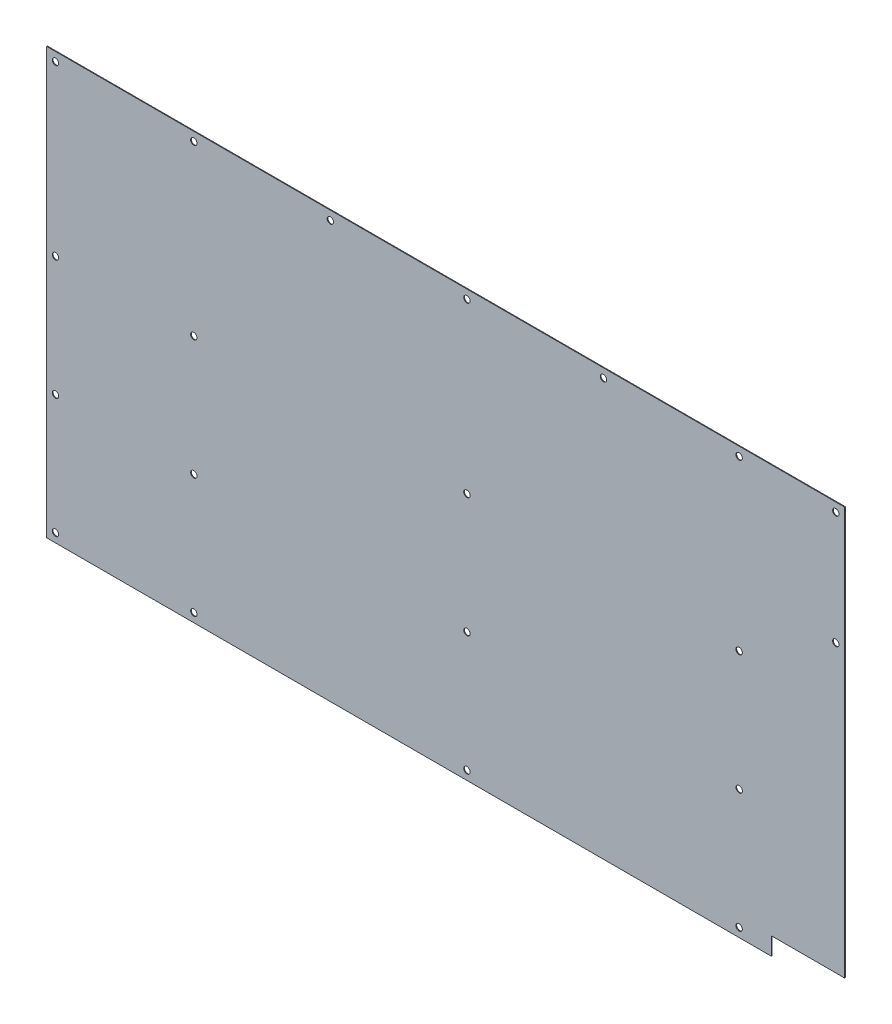
SolidWorks part; units mm, degrees
ref_plane "Front Plane" through (0, 0, 0) normal (0, 0, 1) x (1, 0, 0)
ref_plane "Top Plane" through (0, 0, 0) normal (0, 1, 0) x (1, 0, 0)
ref_plane "Right Plane" through (0, 0, 0) normal (1, 0, 0) x (0, 0, -1)
sketch "Model" plane through (0, 0, 0) normal (0, 0, 1) x (1, 0, 0)
  line L0 (0, 0) -> (415.29, 0)
  line L1 (415.29, 0) -> (415.29, 10.16)
  line L2 (415.29, 10.16) -> (457.2, 10.16)
  line L3 (457.2, 10.16) -> (457.2, 243.84)
  line L4 (457.2, 243.84) -> (0, 243.84)
  line L5 (0, 243.84) -> (0, 0)
  line L276 (452.12, 173.736) -> (452.12, 174.244)
  line L277 (451.866, 173.99) -> (452.374, 173.99)
  line L278 (452.12, 173.736) -> (452.12, 174.244)
  line L279 (451.866, 173.99) -> (452.374, 173.99)
  line L280 (452.12, 173.736) -> (452.12, 174.244)
  line L281 (451.866, 173.99) -> (452.374, 173.99)
  line L282 (452.12, 173.736) -> (452.12, 174.244)
  line L283 (451.866, 173.99) -> (452.374, 173.99)
  line L284 (452.12, 173.736) -> (452.12, 174.244)
  line L285 (451.866, 173.99) -> (452.374, 173.99)
  line L286 (452.12, 173.736) -> (452.12, 174.244)
  line L287 (451.866, 173.99) -> (452.374, 173.99)
  line L288 (452.12, 173.736) -> (452.12, 174.244)
  line L289 (451.866, 173.99) -> (452.374, 173.99)
  line L290 (452.12, 173.736) -> (452.12, 174.244)
  line L291 (451.866, 173.99) -> (452.374, 173.99)
  line L292 (452.12, 238.506) -> (452.12, 239.014)
  line L293 (451.866, 238.76) -> (452.374, 238.76)
  line L294 (452.12, 238.506) -> (452.12, 239.014)
  line L295 (451.866, 238.76) -> (452.374, 238.76)
  line L296 (452.12, 238.506) -> (452.12, 239.014)
  line L297 (451.866, 238.76) -> (452.374, 238.76)
  line L298 (452.12, 238.506) -> (452.12, 239.014)
  line L299 (451.866, 238.76) -> (452.374, 238.76)
  line L300 (452.12, 238.506) -> (452.12, 239.014)
  line L301 (451.866, 238.76) -> (452.374, 238.76)
  line L302 (452.12, 238.506) -> (452.12, 239.014)
  line L303 (451.866, 238.76) -> (452.374, 238.76)
  line L304 (452.12, 238.506) -> (452.12, 239.014)
  line L305 (451.866, 238.76) -> (452.374, 238.76)
  line L306 (452.12, 238.506) -> (452.12, 239.014)
  line L307 (451.866, 238.76) -> (452.374, 238.76)
  line L356 (5.08, 238.506) -> (5.08, 239.014)
  line L357 (4.826, 238.76) -> (5.334, 238.76)
  line L358 (5.08, 238.506) -> (5.08, 239.014)
  line L359 (4.826, 238.76) -> (5.334, 238.76)
  line L360 (5.08, 238.506) -> (5.08, 239.014)
  line L361 (4.826, 238.76) -> (5.334, 238.76)
  line L362 (5.08, 238.506) -> (5.08, 239.014)
  line L363 (4.826, 238.76) -> (5.334, 238.76)
  line L364 (5.08, 238.506) -> (5.08, 239.014)
  line L365 (4.826, 238.76) -> (5.334, 238.76)
  line L366 (5.08, 238.506) -> (5.08, 239.014)
  line L367 (4.826, 238.76) -> (5.334, 238.76)
  line L368 (5.08, 238.506) -> (5.08, 239.014)
  line L369 (4.826, 238.76) -> (5.334, 238.76)
  line L370 (5.08, 238.506) -> (5.08, 239.014)
  line L371 (4.826, 238.76) -> (5.334, 238.76)
  line L372 (84.328, 4.826) -> (84.328, 5.334)
  line L373 (84.074, 5.08) -> (84.582, 5.08)
  line L374 (84.328, 4.826) -> (84.328, 5.334)
  line L375 (84.074, 5.08) -> (84.582, 5.08)
  line L376 (84.328, 4.826) -> (84.328, 5.334)
  line L377 (84.074, 5.08) -> (84.582, 5.08)
  line L378 (84.328, 4.826) -> (84.328, 5.334)
  line L379 (84.074, 5.08) -> (84.582, 5.08)
  line L380 (84.328, 4.826) -> (84.328, 5.334)
  line L381 (84.074, 5.08) -> (84.582, 5.08)
  line L382 (84.328, 4.826) -> (84.328, 5.334)
  line L383 (84.074, 5.08) -> (84.582, 5.08)
  line L384 (84.328, 4.826) -> (84.328, 5.334)
  line L385 (84.074, 5.08) -> (84.582, 5.08)
  line L386 (84.328, 4.826) -> (84.328, 5.334)
  line L387 (84.074, 5.08) -> (84.582, 5.08)
  line L388 (84.328, 73.406) -> (84.328, 73.914)
  line L389 (84.074, 73.66) -> (84.582, 73.66)
  line L390 (84.328, 73.406) -> (84.328, 73.914)
  line L391 (84.074, 73.66) -> (84.582, 73.66)
  line L392 (84.328, 73.406) -> (84.328, 73.914)
  line L393 (84.074, 73.66) -> (84.582, 73.66)
  line L394 (84.328, 73.406) -> (84.328, 73.914)
  line L395 (84.074, 73.66) -> (84.582, 73.66)
  line L396 (84.328, 73.406) -> (84.328, 73.914)
  line L397 (84.074, 73.66) -> (84.582, 73.66)
  line L398 (84.328, 73.406) -> (84.328, 73.914)
  line L399 (84.074, 73.66) -> (84.582, 73.66)
  line L400 (84.328, 73.406) -> (84.328, 73.914)
  line L401 (84.074, 73.66) -> (84.582, 73.66)
  line L402 (84.328, 73.406) -> (84.328, 73.914)
  line L403 (84.074, 73.66) -> (84.582, 73.66)
  line L404 (84.328, 141.986) -> (84.328, 142.494)
  line L405 (84.074, 142.24) -> (84.582, 142.24)
  line L406 (84.328, 141.986) -> (84.328, 142.494)
  line L407 (84.074, 142.24) -> (84.582, 142.24)
  line L408 (84.328, 141.986) -> (84.328, 142.494)
  line L409 (84.074, 142.24) -> (84.582, 142.24)
  line L410 (84.328, 141.986) -> (84.328, 142.494)
  line L411 (84.074, 142.24) -> (84.582, 142.24)
  line L412 (84.328, 141.986) -> (84.328, 142.494)
  line L413 (84.074, 142.24) -> (84.582, 142.24)
  line L414 (84.328, 141.986) -> (84.328, 142.494)
  line L415 (84.074, 142.24) -> (84.582, 142.24)
  line L416 (84.328, 141.986) -> (84.328, 142.494)
  line L417 (84.074, 142.24) -> (84.582, 142.24)
  line L418 (84.328, 141.986) -> (84.328, 142.494)
  line L419 (84.074, 142.24) -> (84.582, 142.24)
  line L420 (84.328, 238.506) -> (84.328, 239.014)
  line L421 (84.074, 238.76) -> (84.582, 238.76)
  line L422 (84.328, 238.506) -> (84.328, 239.014)
  line L423 (84.074, 238.76) -> (84.582, 238.76)
  line L424 (84.328, 238.506) -> (84.328, 239.014)
  line L425 (84.074, 238.76) -> (84.582, 238.76)
  line L426 (84.328, 238.506) -> (84.328, 239.014)
  line L427 (84.074, 238.76) -> (84.582, 238.76)
  line L428 (84.328, 238.506) -> (84.328, 239.014)
  line L429 (84.074, 238.76) -> (84.582, 238.76)
  line L430 (84.328, 238.506) -> (84.328, 239.014)
  line L431 (84.074, 238.76) -> (84.582, 238.76)
  line L432 (84.328, 238.506) -> (84.328, 239.014)
  line L433 (84.074, 238.76) -> (84.582, 238.76)
  line L434 (84.328, 238.506) -> (84.328, 239.014)
  line L435 (84.074, 238.76) -> (84.582, 238.76)
  line L484 (162.56, 238.506) -> (162.56, 239.014)
  line L485 (162.306, 238.76) -> (162.814, 238.76)
  line L486 (162.56, 238.506) -> (162.56, 239.014)
  line L487 (162.306, 238.76) -> (162.814, 238.76)
  line L488 (162.56, 238.506) -> (162.56, 239.014)
  line L489 (162.306, 238.76) -> (162.814, 238.76)
  line L490 (162.56, 238.506) -> (162.56, 239.014)
  line L491 (162.306, 238.76) -> (162.814, 238.76)
  line L492 (162.56, 238.506) -> (162.56, 239.014)
  line L493 (162.306, 238.76) -> (162.814, 238.76)
  line L494 (162.56, 238.506) -> (162.56, 239.014)
  line L495 (162.306, 238.76) -> (162.814, 238.76)
  line L496 (162.56, 238.506) -> (162.56, 239.014)
  line L497 (162.306, 238.76) -> (162.814, 238.76)
  line L498 (162.56, 238.506) -> (162.56, 239.014)
  line L499 (162.306, 238.76) -> (162.814, 238.76)
  line L500 (240.7699, 4.827) -> (240.8141, 5.333)
  line L501 (240.539, 5.1021) -> (241.045, 5.0579)
  line L502 (240.7699, 4.827) -> (240.8141, 5.333)
  line L503 (240.539, 5.1021) -> (241.045, 5.0579)
  line L504 (240.7699, 4.827) -> (240.8141, 5.333)
  line L505 (240.539, 5.1021) -> (241.045, 5.0579)
  line L506 (240.7699, 4.827) -> (240.8141, 5.333)
  line L507 (240.539, 5.1021) -> (241.045, 5.0579)
  line L508 (240.7699, 4.827) -> (240.8141, 5.333)
  line L509 (240.539, 5.1021) -> (241.045, 5.0579)
  line L510 (240.7699, 4.827) -> (240.8141, 5.333)
  line L511 (240.539, 5.1021) -> (241.045, 5.0579)
  line L512 (240.7699, 4.827) -> (240.8141, 5.333)
  line L513 (240.539, 5.1021) -> (241.045, 5.0579)
  line L514 (240.7699, 4.827) -> (240.8141, 5.333)
  line L515 (240.539, 5.1021) -> (241.045, 5.0579)
  line L516 (240.792, 73.406) -> (240.792, 73.914)
  line L517 (240.538, 73.66) -> (241.046, 73.66)
  line L518 (240.792, 73.406) -> (240.792, 73.914)
  line L519 (240.538, 73.66) -> (241.046, 73.66)
  line L520 (240.792, 73.406) -> (240.792, 73.914)
  line L521 (240.538, 73.66) -> (241.046, 73.66)
  line L522 (240.792, 73.406) -> (240.792, 73.914)
  line L523 (240.538, 73.66) -> (241.046, 73.66)
  line L524 (240.792, 73.406) -> (240.792, 73.914)
  line L525 (240.538, 73.66) -> (241.046, 73.66)
  line L526 (240.792, 73.406) -> (240.792, 73.914)
  line L527 (240.538, 73.66) -> (241.046, 73.66)
  line L528 (240.792, 73.406) -> (240.792, 73.914)
  line L529 (240.538, 73.66) -> (241.046, 73.66)
  line L530 (240.792, 73.406) -> (240.792, 73.914)
  line L531 (240.538, 73.66) -> (241.046, 73.66)
  line L532 (240.792, 141.986) -> (240.792, 142.494)
  line L533 (240.538, 142.24) -> (241.046, 142.24)
  line L534 (240.792, 141.986) -> (240.792, 142.494)
  line L535 (240.538, 142.24) -> (241.046, 142.24)
  line L536 (240.792, 141.986) -> (240.792, 142.494)
  line L537 (240.538, 142.24) -> (241.046, 142.24)
  line L538 (240.792, 141.986) -> (240.792, 142.494)
  line L539 (240.538, 142.24) -> (241.046, 142.24)
  line L540 (240.792, 141.986) -> (240.792, 142.494)
  line L541 (240.538, 142.24) -> (241.046, 142.24)
  line L542 (240.792, 141.986) -> (240.792, 142.494)
  line L543 (240.538, 142.24) -> (241.046, 142.24)
  line L544 (240.792, 141.986) -> (240.792, 142.494)
  line L545 (240.538, 142.24) -> (241.046, 142.24)
  line L546 (240.792, 141.986) -> (240.792, 142.494)
  line L547 (240.538, 142.24) -> (241.046, 142.24)
  line L548 (240.792, 238.506) -> (240.792, 239.014)
  line L549 (240.538, 238.76) -> (241.046, 238.76)
  line L550 (240.792, 238.506) -> (240.792, 239.014)
  line L551 (240.538, 238.76) -> (241.046, 238.76)
  line L552 (240.792, 238.506) -> (240.792, 239.014)
  line L553 (240.538, 238.76) -> (241.046, 238.76)
  line L554 (240.792, 238.506) -> (240.792, 239.014)
  line L555 (240.538, 238.76) -> (241.046, 238.76)
  line L556 (240.792, 238.506) -> (240.792, 239.014)
  line L557 (240.538, 238.76) -> (241.046, 238.76)
  line L558 (240.792, 238.506) -> (240.792, 239.014)
  line L559 (240.538, 238.76) -> (241.046, 238.76)
  line L560 (240.792, 238.506) -> (240.792, 239.014)
  line L561 (240.538, 238.76) -> (241.046, 238.76)
  line L562 (240.792, 238.506) -> (240.792, 239.014)
  line L563 (240.538, 238.76) -> (241.046, 238.76)
  line L612 (319.024, 238.506) -> (319.024, 239.014)
  line L613 (318.77, 238.76) -> (319.278, 238.76)
  line L614 (319.024, 238.506) -> (319.024, 239.014)
  line L615 (318.77, 238.76) -> (319.278, 238.76)
  line L616 (319.024, 238.506) -> (319.024, 239.014)
  line L617 (318.77, 238.76) -> (319.278, 238.76)
  line L618 (319.024, 238.506) -> (319.024, 239.014)
  line L619 (318.77, 238.76) -> (319.278, 238.76)
  line L620 (319.024, 238.506) -> (319.024, 239.014)
  line L621 (318.77, 238.76) -> (319.278, 238.76)
  line L622 (319.024, 238.506) -> (319.024, 239.014)
  line L623 (318.77, 238.76) -> (319.278, 238.76)
  line L624 (319.024, 238.506) -> (319.024, 239.014)
  line L625 (318.77, 238.76) -> (319.278, 238.76)
  line L626 (319.024, 238.506) -> (319.024, 239.014)
  line L627 (318.77, 238.76) -> (319.278, 238.76)
  line L628 (396.748, 4.826) -> (396.748, 5.334)
  line L629 (396.494, 5.08) -> (397.002, 5.08)
  line L630 (396.748, 4.826) -> (396.748, 5.334)
  line L631 (396.494, 5.08) -> (397.002, 5.08)
  line L632 (396.748, 4.826) -> (396.748, 5.334)
  line L633 (396.494, 5.08) -> (397.002, 5.08)
  line L634 (396.748, 4.826) -> (396.748, 5.334)
  line L635 (396.494, 5.08) -> (397.002, 5.08)
  line L636 (396.748, 4.826) -> (396.748, 5.334)
  line L637 (396.494, 5.08) -> (397.002, 5.08)
  line L638 (396.748, 4.826) -> (396.748, 5.334)
  line L639 (396.494, 5.08) -> (397.002, 5.08)
  line L640 (396.748, 4.826) -> (396.748, 5.334)
  line L641 (396.494, 5.08) -> (397.002, 5.08)
  line L642 (396.748, 4.826) -> (396.748, 5.334)
  line L643 (396.494, 5.08) -> (397.002, 5.08)
  line L644 (396.748, 73.406) -> (396.748, 73.914)
  line L645 (396.494, 73.66) -> (397.002, 73.66)
  line L646 (396.748, 73.406) -> (396.748, 73.914)
  line L647 (396.494, 73.66) -> (397.002, 73.66)
  line L648 (396.748, 73.406) -> (396.748, 73.914)
  line L649 (396.494, 73.66) -> (397.002, 73.66)
  line L650 (396.748, 73.406) -> (396.748, 73.914)
  line L651 (396.494, 73.66) -> (397.002, 73.66)
  line L652 (396.748, 73.406) -> (396.748, 73.914)
  line L653 (396.494, 73.66) -> (397.002, 73.66)
  line L654 (396.748, 73.406) -> (396.748, 73.914)
  line L655 (396.494, 73.66) -> (397.002, 73.66)
  line L656 (396.748, 73.406) -> (396.748, 73.914)
  line L657 (396.494, 73.66) -> (397.002, 73.66)
  line L658 (396.748, 73.406) -> (396.748, 73.914)
  line L659 (396.494, 73.66) -> (397.002, 73.66)
  line L660 (396.748, 141.986) -> (396.748, 142.494)
  line L661 (396.494, 142.24) -> (397.002, 142.24)
  line L662 (396.748, 141.986) -> (396.748, 142.494)
  line L663 (396.494, 142.24) -> (397.002, 142.24)
  line L664 (396.748, 141.986) -> (396.748, 142.494)
  line L665 (396.494, 142.24) -> (397.002, 142.24)
  line L666 (396.748, 141.986) -> (396.748, 142.494)
  line L667 (396.494, 142.24) -> (397.002, 142.24)
  line L668 (396.748, 141.986) -> (396.748, 142.494)
  line L669 (396.494, 142.24) -> (397.002, 142.24)
  line L670 (396.748, 141.986) -> (396.748, 142.494)
  line L671 (396.494, 142.24) -> (397.002, 142.24)
  line L672 (396.748, 141.986) -> (396.748, 142.494)
  line L673 (396.494, 142.24) -> (397.002, 142.24)
  line L674 (396.748, 141.986) -> (396.748, 142.494)
  line L675 (396.494, 142.24) -> (397.002, 142.24)
  line L676 (396.748, 238.506) -> (396.748, 239.014)
  line L677 (396.494, 238.76) -> (397.002, 238.76)
  line L678 (396.748, 238.506) -> (396.748, 239.014)
  line L679 (396.494, 238.76) -> (397.002, 238.76)
  line L680 (396.748, 238.506) -> (396.748, 239.014)
  line L681 (396.494, 238.76) -> (397.002, 238.76)
  line L682 (396.748, 238.506) -> (396.748, 239.014)
  line L683 (396.494, 238.76) -> (397.002, 238.76)
  line L684 (396.748, 238.506) -> (396.748, 239.014)
  line L685 (396.494, 238.76) -> (397.002, 238.76)
  line L686 (396.748, 238.506) -> (396.748, 239.014)
  line L687 (396.494, 238.76) -> (397.002, 238.76)
  line L688 (396.748, 238.506) -> (396.748, 239.014)
  line L689 (396.494, 238.76) -> (397.002, 238.76)
  line L690 (396.748, 238.506) -> (396.748, 239.014)
  line L691 (396.494, 238.76) -> (397.002, 238.76)
  circle A0 centre (5.08, 142.24) radius 1.8288
  circle A1 centre (415.29, 0) radius 0.0635
  circle A2 centre (415.29, 10.16) radius 0.0635
  circle A3 centre (457.2, 10.16) radius 0.0635
  circle A4 centre (457.2, 243.84) radius 0.0635
  circle A5 centre (0, 243.84) radius 0.0635
  circle A6 centre (5.08, 73.66) radius 1.8288
  circle A7 centre (5.08, 5.08) radius 1.8288
  circle A66 centre (5.08, 238.76) radius 1.8288
  circle A67 centre (84.328, 238.76) radius 1.8288
  circle A68 centre (162.56, 238.76) radius 1.8288
  circle A69 centre (240.792, 238.76) radius 1.8288
  circle A70 centre (319.024, 238.76) radius 1.8288
  circle A71 centre (396.748, 238.76) radius 1.8288
  circle A72 centre (452.12, 238.76) radius 1.8288
  circle A73 centre (452.12, 173.99) radius 1.8288
  circle A74 centre (396.748, 142.24) radius 1.8288
  circle A76 centre (240.792, 142.24) radius 1.8288
  circle A78 centre (84.328, 142.24) radius 1.8288
  circle A81 centre (84.328, 73.66) radius 1.8288
  circle A83 centre (240.792, 73.66) radius 1.8288
  circle A85 centre (396.748, 73.66) radius 1.8288
  circle A86 centre (396.748, 5.08) radius 1.8288
  circle A88 centre (240.792, 5.08) radius 1.8288
  circle A90 centre (84.328, 5.08) radius 1.8288
  point P1 (5.08, 142.24)
  point P12 (5.08, 73.66)
  point P13 (5.08, 5.08)
  dimension "D1" = 391.668
  dimension "D2" = 77.724
  dimension "D3" = 78.232
  dimension "D4" = 78.232
  dimension "D5" = 78.232
  dimension "D6" = 79.248
  dimension "D7" = 96.52
  dimension "D8" = 68.58
  dimension "D9" = 68.58
  dimension "D10" = 68.58
  dimension "D11" = 68.58
  dimension "D12" = 96.52
  dimension "D13" = 96.52
  dimension "D14" = 68.58
  dimension "D15" = 68.58
  dimension "D16" = 79.248
  dimension "D17" = 79.248
  dimension "D18" = 79.248
  dimension "D19" = 68.58
  dimension "D20" = 68.58
  dimension "D21" = 96.52
extrude "Boss-Extrude2" add sketch "Model" along normal blind 0.4064
